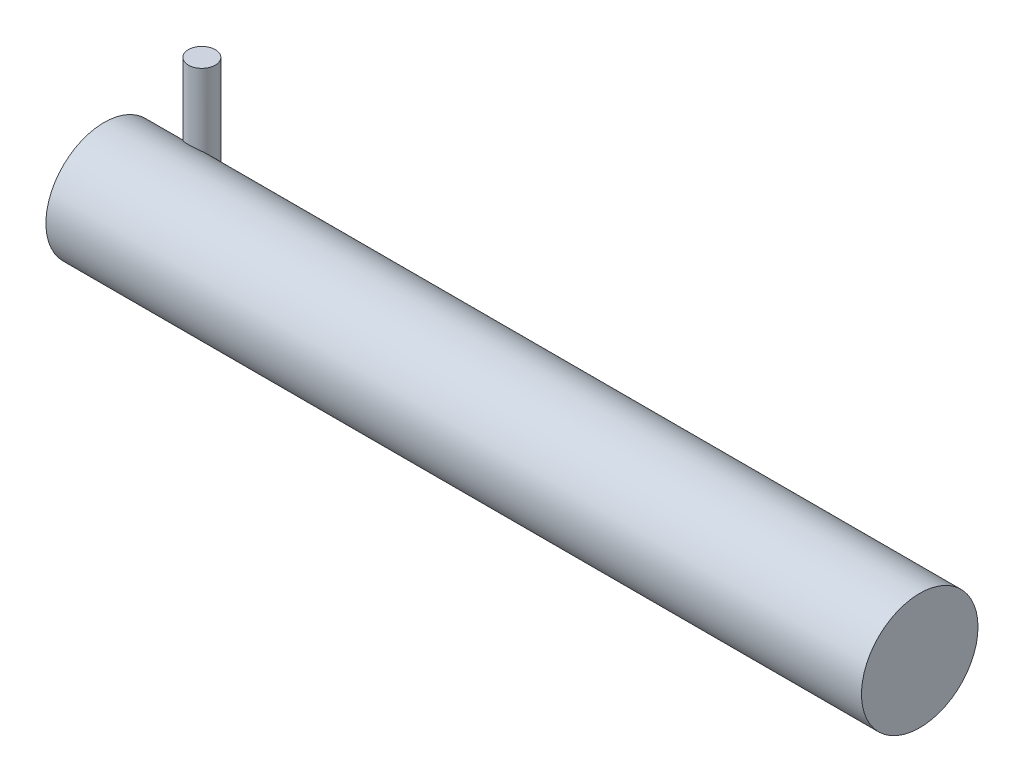
SolidWorks part; units mm, degrees
ref_plane "Front Plane" through (0, 0, 0) normal (0, 0, 1) x (1, 0, 0)
ref_plane "Top Plane" through (0, 0, 0) normal (0, 1, 0) x (1, 0, 0)
ref_plane "Right Plane" through (0, 0, 0) normal (1, 0, 0) x (0, 0, -1)
sketch "Sketch1" plane through (0, 0, 0) normal (1, 0, 0) x (0, 0, -1)
  circle A0 centre (0, 0) radius 5
extrude "Boss-Extrude1" add sketch "Sketch1" along normal blind 70
sketch "Sketch2" plane through (0, 0, 0) normal (0, 1, 0) x (1, 0, 0)
  circle A0 centre (4.3592, 4.0254) radius 1.1545
extrude "Boss-Extrude2" add sketch "Sketch2" along normal blind 10
